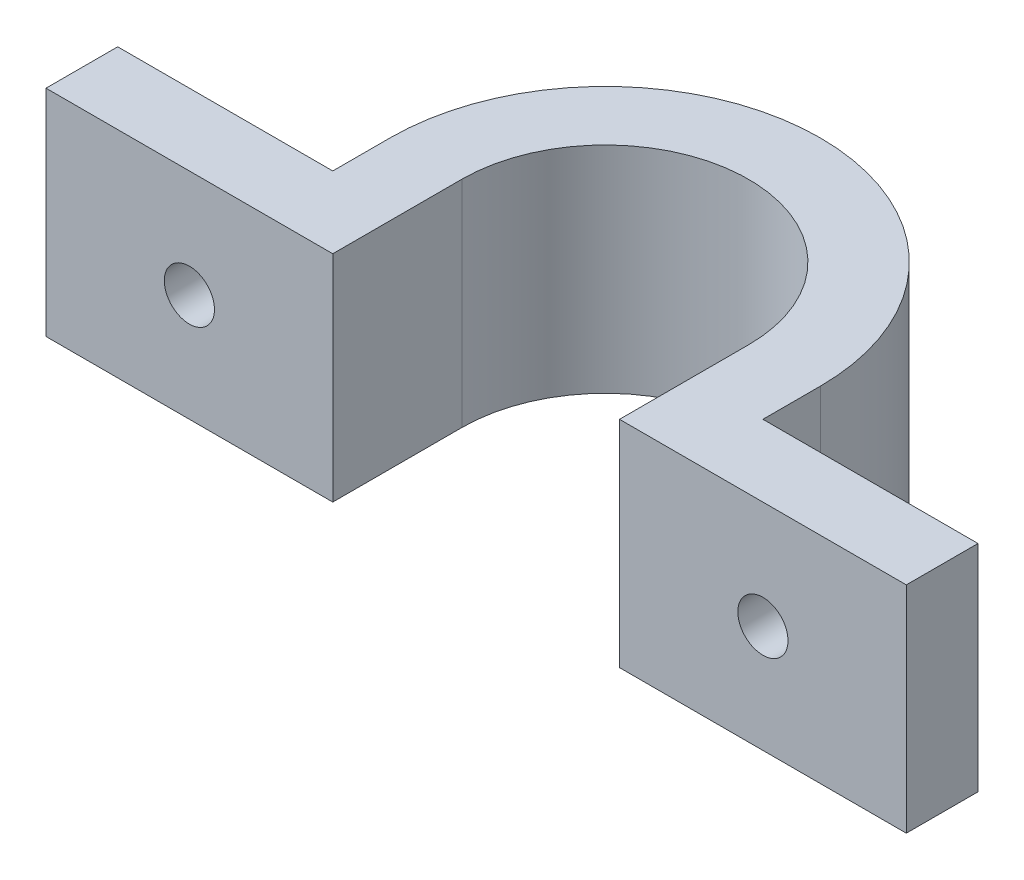
SolidWorks part; units mm, degrees
ref_plane "Front Plane" through (0, 0, 0) normal (0, 0, 1) x (1, 0, 0)
ref_plane "Top Plane" through (0, 0, 0) normal (0, 1, 0) x (1, 0, 0)
ref_plane "Right Plane" through (0, 0, 0) normal (1, 0, 0) x (0, 0, -1)
sketch "Sketch1" plane through (0, 0, 0) normal (0, 1, 0) x (1, 0, 0)
  line L6 (-30, -4) -> (-30, -9)
  line L7 (-30, -9) -> (-10, -9)
  line L8 (-10, -9) -> (-10, 0)
  line L10 (30, -4) -> (30, -9)
  line L11 (30, -9) -> (10, -9)
  line L12 (10, -9) -> (10, 0)
  line L14 (-15, 0) -> (-15, -4)
  line L15 (-15, -4) -> (-30, -4)
  line L16 (15, 0) -> (15, -4)
  line L17 (15, -4) -> (30, -4)
  arc A0 (15, 0) -> (-15, 0) centre (0, 0) ccw
  arc A1 (-10, 0) -> (10, 0) centre (0, 0) cw
  point P12 (0, -10)
  dimension "D1" = 10
  dimension "D2" = 5
  dimension "D5" = 1
  dimension "D3" = 5
  dimension "D4" = 15
extrude "Boss-Extrude1" add sketch "Sketch1" along normal blind 15
sketch "Sketch2" plane through (0, 0, 4) normal (0, 0, -1) x (-1, 0, 0)
  line L0 (-30, 7.5) -> (-20, 7.5) construction
  line L2 (30, 7.5) -> (20, 7.5) construction
  line L4 (-30, 15) -> (-30, 0) construction
  line L5 (30, 15) -> (30, 0) construction
  circle A0 centre (-20, 7.5) radius 1.75
  circle A1 centre (20, 7.5) radius 1.75
  dimension "D1" = 3.5
  dimension "D2" = 40
extrude "Cut-Extrude1" cut sketch "Sketch2" against normal through all
